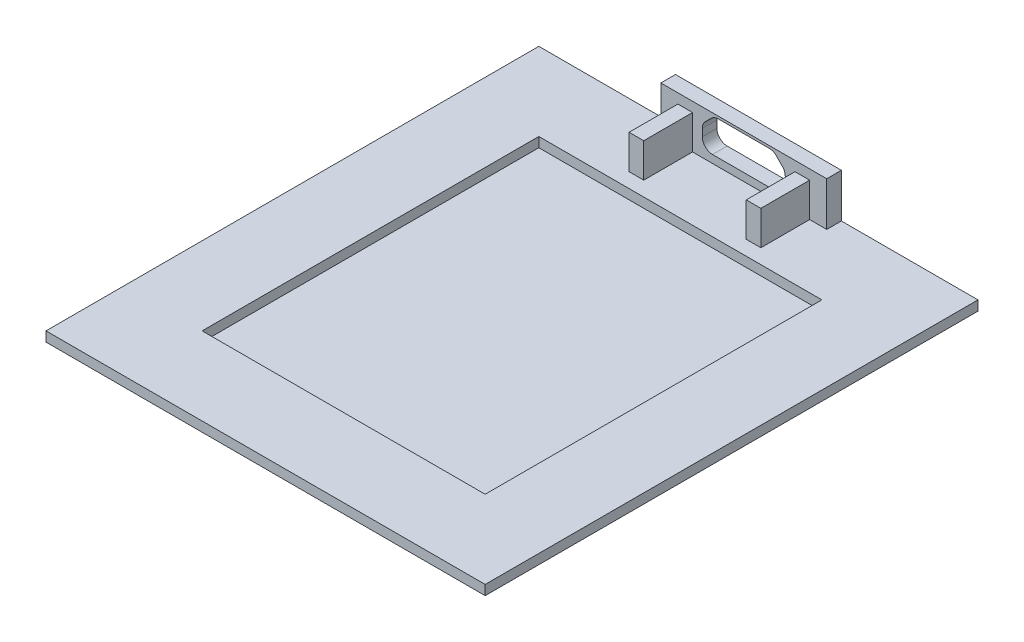
SolidWorks part; units mm, degrees
ref_plane "Alzado" through (0, 0, 0) normal (0, 0, 1) x (1, 0, 0)
ref_plane "Planta" through (0, 0, 0) normal (0, 1, 0) x (1, 0, 0)
ref_plane "Vista lateral" through (0, 0, 0) normal (1, 0, 0) x (0, 0, -1)
sketch "Croquis1" plane through (0, 0, 0) normal (0, 1, 0) x (1, 0, 0)
  line L1 (0, 0) -> (45, 0)
  line L2 (0, 0) -> (0, -50.5)
  line L3 (0, -50.5) -> (45, -50.5)
  line L4 (45, 0) -> (45, -50.5)
  dimension "D1" = 45
  dimension "D2" = 50.5
extrude "Saliente-Extruir1" add sketch "Croquis1" along normal blind 2
sketch "Croquis10" plane through (0, 2, 0) normal (0, 1, 0) x (1, 0, 0)
  line L15 (37, -42.5) -> (37, -8)
  line L16 (8, -42.5) -> (37, -42.5)
  line L17 (8, -8) -> (8, -42.5)
  line L18 (37, -8) -> (8, -8)
  line L19 (37, -42.5) -> (37, -8)
  line L20 (8, -42.5) -> (37, -42.5)
  line L21 (8, -8) -> (8, -42.5)
  line L22 (37, -8) -> (8, -8)
  dimension "D1" = 8
extrude "Cortar-Extruir5" cut sketch "Croquis10" against normal blind 1
sketch "Croquis11" plane through (0, 0, 0) normal (0, -1, 0) x (1, 0, 0)
  line L0 (45, 0) -> (45, 50.5)
  line L1 (45, 50.5) -> (45, 0) construction
  line L2 (45, 50.5) -> (0, 50.5)
  line L3 (0, 50.5) -> (0, 0)
  line L4 (0, 0) -> (1, 0)
  line L5 (45, 0) -> (0, 0) construction
  line L6 (1, 0) -> (1, 49.5)
  line L7 (1, 49.5) -> (44, 49.5)
  line L8 (44, 49.5) -> (44, 0)
  line L9 (44, 0) -> (45, 0)
  dimension "D1" = 1
  dimension "D2" = 1
  dimension "D3" = 1
extrude "Cortar-Extruir6" cut sketch "Croquis11" against normal blind 1
sketch "Croquis6" plane through (0, 0, 0) normal (0, 0, -1) x (-1, 0, 0)
  line L1 (-45, 2) -> (0, 2) construction
  line L4 (-14, 2) -> (-31, 2)
  line L5 (-14, 2) -> (-14, 6.5)
  line L6 (-14, 6.5) -> (-31, 6.5)
  line L7 (-31, 2) -> (-31, 6.5)
  point P4 (-22.5, 2)
  point P7 (-22.5, 2)
  dimension "D1" = 4.5
  dimension "D2" = 17
extrude "Saliente-Extruir5" add sketch "Croquis6" against normal blind 1.5
sketch "Croquis8" plane through (0, 0, 0) normal (0, 0, -1) x (-1, 0, 0)
  line L0 (-22.5, 2.8) -> (-22.5, 6.25) construction
  line L1 (-19.1611, 5.9425) -> (-18.5575, 5.3389)
  line L2 (-18.25, 3.85) -> (-18.25, 4.5964)
  line L4 (-44, 0) -> (-1, 0) construction
  line L5 (-14, 6.5) -> (-31, 6.5) construction
  line L15 (-19.3, 2.8) -> (-25.7, 2.8)
  line L16 (-26.75, 3.85) -> (-26.75, 4.5964)
  line L17 (-25.8389, 5.9425) -> (-26.4425, 5.3389)
  line L18 (-25.0964, 6.25) -> (-19.9036, 6.25)
  arc A0 (-19.9036, 6.25) -> (-19.1611, 5.9425) centre (-19.9036, 5.2) cw
  arc A1 (-18.5575, 5.3389) -> (-18.25, 4.5964) centre (-19.3, 4.5964) cw
  arc A2 (-18.25, 3.85) -> (-19.3, 2.8) centre (-19.3, 3.85) cw
  arc A12 (-26.75, 3.85) -> (-25.7, 2.8) centre (-25.7, 3.85) ccw
  arc A13 (-26.4425, 5.3389) -> (-26.75, 4.5964) centre (-25.7, 4.5964) ccw
  arc A14 (-25.0964, 6.25) -> (-25.8389, 5.9425) centre (-25.0964, 5.2) ccw
  point P0 (-22.5, 2.8)
  point P1 (-22.5, 6.25)
  point P13 (-22.5, 0)
  dimension "D1" = 3.45
  dimension "D3" = 1.7964
  dimension "D5" = 0.3075
  dimension "D7" = 1.05
  dimension "D9" = 4.25
  dimension "D11" = 3.9425
  dimension "D6" = 1.05
  dimension "D8" = 1.05
  dimension "D2" = 1.05
  dimension "D4" = 2.5389
  dimension "D10" = 4.25
  dimension "D12" = 3.3389
  dimension "D13" = 2.5964
  dimension "D14" = 3.2
  dimension "D15" = 0.25
extrude "Cortar-Extruir4" cut sketch "Croquis8" against normal up to next
sketch "Croquis9" plane through (0, 0, 1.5) normal (0, 0, 1) x (1, 0, 0)
  line L0 (19.3, 2.8) -> (25.7, 2.8) construction
  line L1 (22.5, 2.8) -> (22.5, 2) construction
  line L2 (31, 2) -> (14, 2) construction
  line L3 (14, 6.5) -> (31, 6.5) construction
  line L6 (27.75, 2) -> (29.25, 2)
  line L7 (27.75, 2) -> (27.75, 5.5)
  line L8 (27.75, 5.5) -> (29.25, 5.5)
  line L9 (29.25, 2) -> (29.25, 5.5)
  line L10 (26.75, 3.85) -> (26.75, 4.5964) construction
  line L11 (17.25, 2) -> (15.75, 2)
  line L12 (15.75, 2) -> (15.75, 5.5)
  line L13 (17.25, 5.5) -> (15.75, 5.5)
  line L14 (17.25, 2) -> (17.25, 5.5)
  point P0 (22.5, 2.8)
  dimension "D1" = 1
  dimension "D2" = 1.5
  dimension "D3" = 1
extrude "Saliente-Extruir6" add sketch "Croquis9" along normal blind 5
